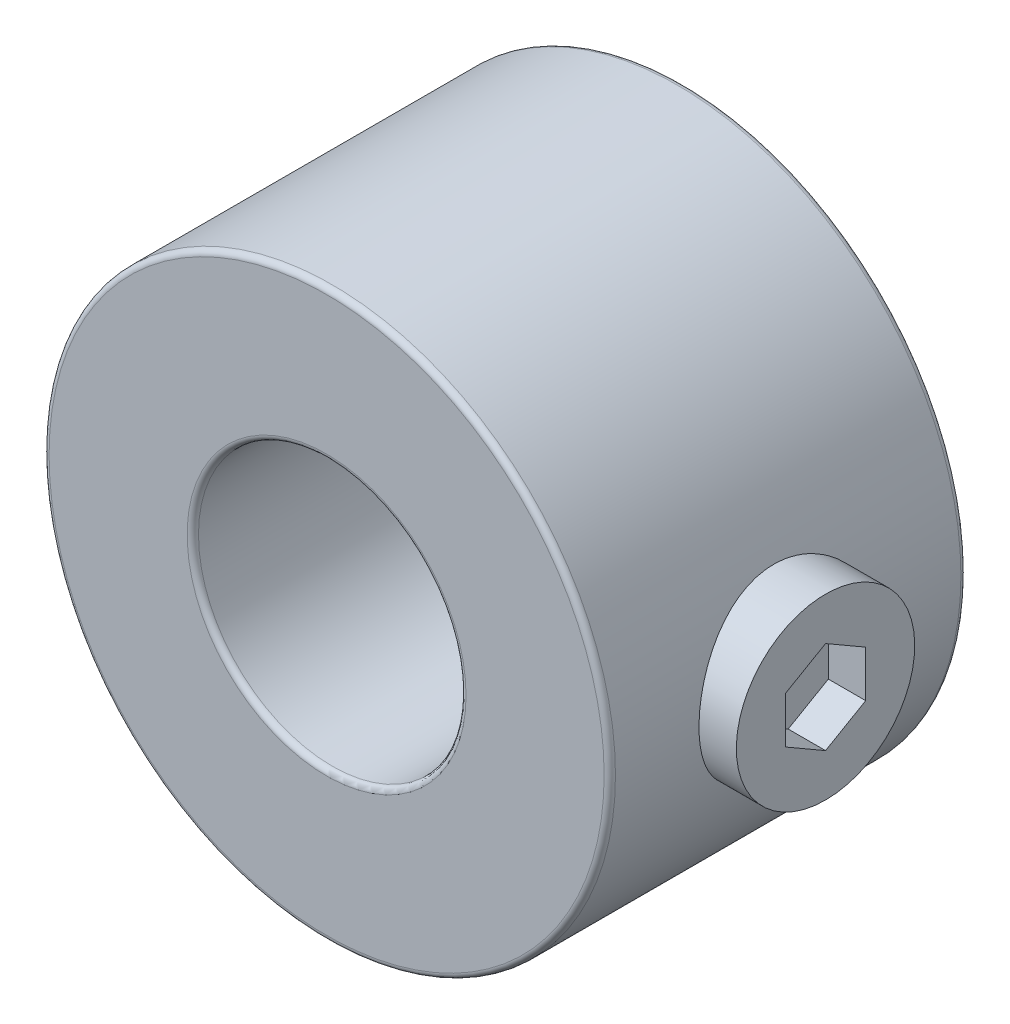
SolidWorks part; units mm, degrees
ref_plane "Front Plane" through (0, 0, 0) normal (0, 0, 1) x (1, 0, 0)
ref_plane "Top Plane" through (0, 0, 0) normal (0, 1, 0) x (1, 0, 0)
ref_plane "Right Plane" through (0, 0, 0) normal (1, 0, 0) x (0, 0, -1)
sketch "Sketch1" plane through (0, 0, 0) normal (0, 0, 1) x (1, 0, 0)
  circle A0 centre (0, 0) radius 6.35
  circle A1 centre (0, 0) radius 3
  point P4 (6.35, 0)
  dimension "Bore Dia" = 6
  dimension "OD" = 12.7
extrude "Extrude1" add sketch "Sketch1" along normal blind 8
ref_plane "Plane1" through (6.35, 0, 0) normal (1, 0, 0) x (0, 0, -1)
sketch "Sketch2" plane through (6.35, 0, 0) normal (1, 0, 0) x (0, 0, -1)
  line L0 (0, 0) -> (-8, 0) construction
  line L1 (-8, 6.35) -> (-8, -6.35) construction
  circle A0 centre (-4, 0) radius 2
  dimension "Set Screw Dia" = 4
extrude "Cut-Extrude1" cut sketch "Sketch2" against normal up to surface (6.35 mm away) up to plane "Right Plane"
ref_plane "Plane2" through (0, 0, 4) normal (0, 0, 1) x (1, 0, 0)
sketch "Sketch3" plane through (0, 0, 4) normal (0, 0, 1) x (1, 0, 0)
  line L1 (3.8375, 0) -> (7.1875, 0)
  line L2 (3.8375, 0) -> (3.8375, 2)
  line L3 (3.8375, 2) -> (7.1875, 2)
  line L4 (7.1875, 0) -> (7.1875, 2)
  line L5 (3.8375, 0) -> (0, 0) construction
  dimension "D1" = 3.35
  dimension "D2" = 0.8375
  dimension "D3" = 4
revolve "Revolve1" add sketch "Sketch3" angle 360 about L1
sketch "Sketch4" plane through (7.1875, 0, 0) normal (1, 0, 0) x (0, 0, -1)
  line L1 (-4, 1.0392) -> (-4.9, 0.5196)
  line L2 (-4.9, 0.5196) -> (-4.9, -0.5196)
  line L3 (-4.9, -0.5196) -> (-4, -1.0392)
  line L4 (-4, -1.0392) -> (-3.1, -0.5196)
  line L5 (-3.1, -0.5196) -> (-3.1, 0.5196)
  line L6 (-3.1, 0.5196) -> (-4, 1.0392)
  circle A0 centre (-4, 0) radius 0.9 construction
  dimension "D1" = 1.8
extrude "Cut-Extrude2" cut sketch "Sketch4" against normal up to vertex (0.8375 mm away) up to point (6.35, 0, 4)
fillet "Fillet1" radius 0.127 4 edges at (3, 0, 0) (3, 0, 8) (6.35, 0, 0) (6.35, 0, 8)
equation "\"D1@Sketch3\" = (\"OD@Sketch1\"-\"Bore Dia@Sketch1\")/2"
equation "\"D2@Sketch3\" = \"D1@Sketch3\"/4"
equation "\"D1@Sketch4\" = \"Set Screw Dia@Sketch2\"*.45"
equation "\"D3@Sketch3\" = \"Set Screw Dia@Sketch2\""
equation "\"D1@Fillet1\" = \"OD@Sketch1\"*.01"
